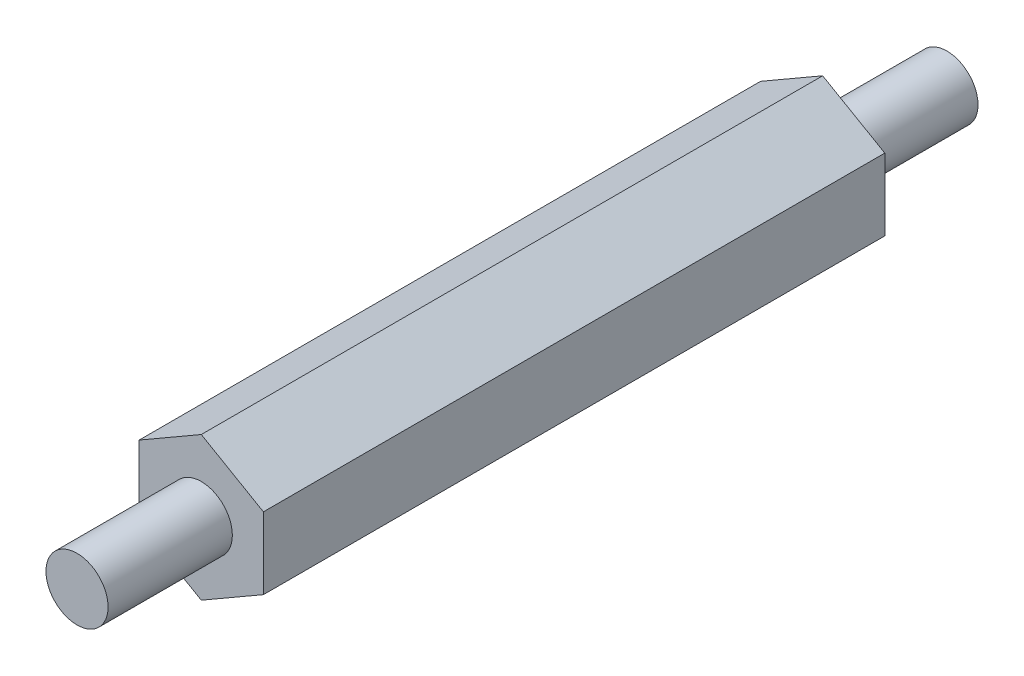
SolidWorks part; units mm, degrees
ref_plane "Front Plane" through (0, 0, 0) normal (0, 0, 1) x (1, 0, 0)
ref_plane "Top Plane" through (0, 0, 0) normal (0, 1, 0) x (1, 0, 0)
ref_plane "Right Plane" through (0, 0, 0) normal (1, 0, 0) x (0, 0, -1)
sketch "Sketch1" plane through (0, 0, 0) normal (0, 0, 1) x (1, 0, 0)
  line L1 (-0.9186, -3.3315) -> (2.0814, -1.5995)
  line L2 (2.0814, -1.5995) -> (2.0814, 1.8646)
  line L3 (2.0814, 1.8646) -> (-0.9186, 3.5967)
  line L4 (-0.9186, 3.5967) -> (-3.9186, 1.8646)
  line L5 (-3.9186, 1.8646) -> (-3.9186, -1.5995)
  line L6 (-3.9186, -1.5995) -> (-0.9186, -3.3315)
  circle A0 centre (-0.9186, 0.1326) radius 3 construction
  dimension "D1" = 6
extrude "Boss-Extrude1" add sketch "Sketch1" along normal blind 30 contours L4 L5 L6 L1 L2 L3
sketch "Sketch2" plane through (0, 0, 30) normal (0, 0, 1) x (1, 0, 0)
  circle A0 centre (-0.9186, 0.1326) radius 1.5
extrude "Boss-Extrude2" add sketch "Sketch2" along normal blind 6
sketch "Sketch3" plane through (0, 0, 0) normal (0, 0, -1) x (-1, 0, 0)
  circle A0 centre (0.9186, 0.1326) radius 1.5
extrude "Boss-Extrude3" add sketch "Sketch3" along normal blind 6
